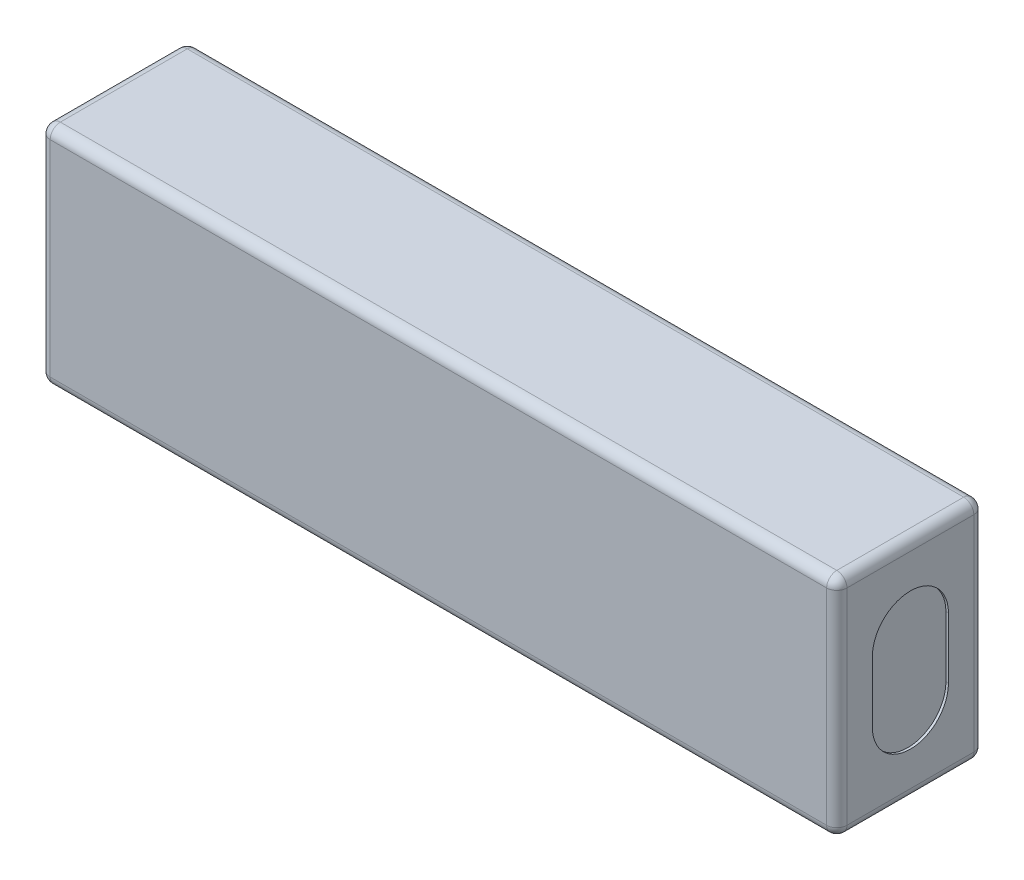
SolidWorks part; units mm, degrees
ref_plane "Plano frontal" through (0, 0, 0) normal (0, 0, 1) x (1, 0, 0)
ref_plane "Plano superior" through (0, 0, 0) normal (0, 1, 0) x (1, 0, 0)
ref_plane "Plano direito" through (0, 0, 0) normal (1, 0, 0) x (0, 0, -1)
sketch "Esboço1" plane through (0, 0, 0) normal (0, 0, 1) x (1, 0, 0)
  line L1 (-78.5, 22.25) -> (78.5, 22.25)
  line L2 (-78.5, 22.25) -> (-78.5, -22.25)
  line L3 (-78.5, -22.25) -> (78.5, -22.25)
  line L4 (78.5, 22.25) -> (78.5, -22.25)
  line L5 (-78.5, 22.25) -> (78.5, -22.25) construction
  line L6 (-78.5, -22.25) -> (78.5, 22.25) construction
  point P0 (0, 0)
  dimension "D1" = 157
  dimension "D2" = 44.5
extrude "Ressalto-extrusão1" add sketch "Esboço1" along normal mid plane 29
sketch "Esboço2" plane through (78.5, 0, 0) normal (1, 0, 0) x (0, 0, -1)
  line L0 (0, 22.25) -> (0, -22.25) construction
  line L1 (-14.5, 22.25) -> (14.5, 22.25) construction
  line L2 (-14.5, -22.25) -> (14.5, -22.25) construction
  line L3 (0, 0) -> (-14.5, 0) construction
  line L4 (-14.5, -22.25) -> (-14.5, 22.25) construction
  line L5 (0, 6) -> (0, -6) construction
  line L6 (7.5, 6) -> (7.5, -6)
  line L7 (-7.5, 6) -> (-7.5, -6)
  arc A0 (7.5, 6) -> (-7.5, 6) centre (0, 6) ccw
  arc A1 (-7.5, -6) -> (7.5, -6) centre (0, -6) ccw
  point P13 (0, 0)
  dimension "D1" = 12
  dimension "D2" = 15
extrude "Corte-extrusão1" cut sketch "Esboço2" against normal blind 0.5
mirror "Espelhar1" about plane through (0, 0, 0) normal (1, 0, 0) of "Corte-extrusão1"
fillet "Filete1" radius 2 12 edges at (-78.5, -22.25, 0) (78.5, -22.25, 0) (-78.5, 0, -14.5) (0, -22.25, -14.5) (78.5, 0, -14.5) (78.5, 22.25, 0) (-78.5, 22.25, 0) (0, 22.25, -14.5) (0, -22.25, 14.5) (-78.5, 0, 14.5) (0, 22.25, 14.5) (78.5, 0, 14.5)
